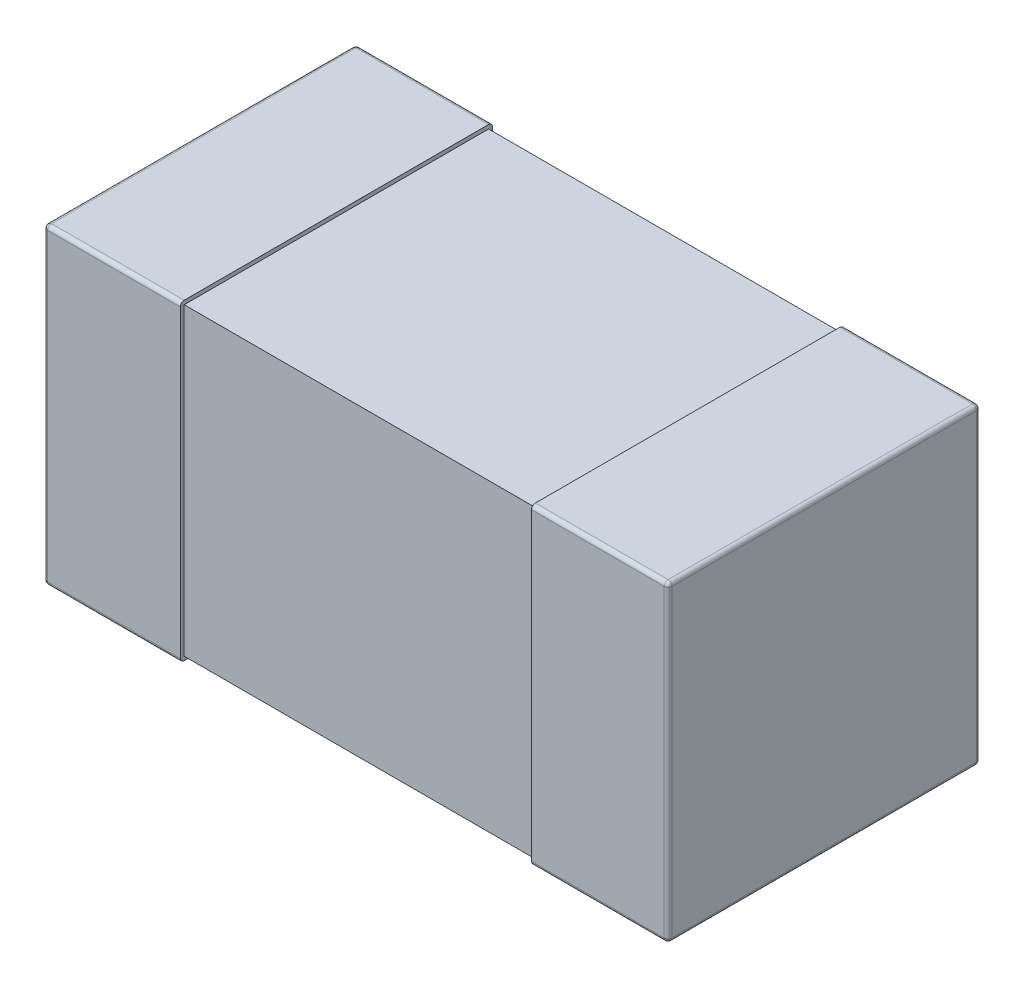
SolidWorks part; units mm, degrees
ref_plane "Front Plane" through (0, 0, 0) normal (0, 0, 1) x (1, 0, 0)
ref_plane "Top Plane" through (0, 0, 0) normal (0, 1, 0) x (1, 0, 0)
ref_plane "Right Plane" through (0, 0, 0) normal (1, 0, 0) x (0, 0, -1)
sketch "Sketch1" plane through (0, 0, 0) normal (0, 1, 0) x (1, 0, 0)
  line L0 (0, 0.15) -> (0, -0.15) construction
  line L1 (-0.8, 0) -> (0, 0) construction
  line L3 (-0.8, 0.4) -> (-0.45, 0.4)
  line L4 (-0.8, 0.4) -> (-0.8, -0.4)
  line L5 (-0.8, -0.4) -> (-0.45, -0.4)
  line L6 (-0.45, 0.4) -> (-0.45, -0.4)
  dimension "BANDWIDTH" = 0.35
  dimension "WIDTH" = 0.8
  dimension "LENGTH-HALF" = 0.8
extrude "THICKNESS" add sketch "Sketch1" along normal mid plane 0.8
fillet "Fillet1" radius 0.01 8 edges at (-0.8, -0.4, 0) (-0.625, -0.4, -0.4) (-0.8, 0, -0.4) (-0.625, -0.4, 0.4) (-0.8, 0, 0.4) (-0.8, 0.4, 0) (-0.625, 0.4, -0.4) (-0.625, 0.4, 0.4)
sketch "Sketch2" plane through (0, 0, 0) normal (1, 0, 0) x (0, 0, -1)
  line L0 (0, 0.4) -> (0, -0.4) construction
  line L1 (-0.39, 0.39) -> (0.39, 0.39)
  line L2 (-0.39, 0.39) -> (-0.39, -0.39)
  line L3 (-0.39, -0.39) -> (0.39, -0.39)
  line L4 (0.39, 0.39) -> (0.39, -0.39)
  line L5 (-0.39, 0.4) -> (0.39, 0.4) construction
  line L6 (-0.39, -0.4) -> (0.39, -0.4) construction
  line L7 (-0.4, 0) -> (0.4, 0) construction
  line L8 (-0.4, 0.39) -> (-0.4, -0.39) construction
  line L9 (0.4, 0.39) -> (0.4, -0.39) construction
  dimension "D1" = 0.01
  dimension "D2" = 0.01
extrude "Boss-Extrude2" add sketch "Sketch2" against normal up to surface (0.45 mm away) up to face at (-0.45, 0, 0)
mirror "Mirror3" about plane through (0, 0, 0) normal (1, 0, 0) of "Boss-Extrude2", "Fillet1", "THICKNESS"
